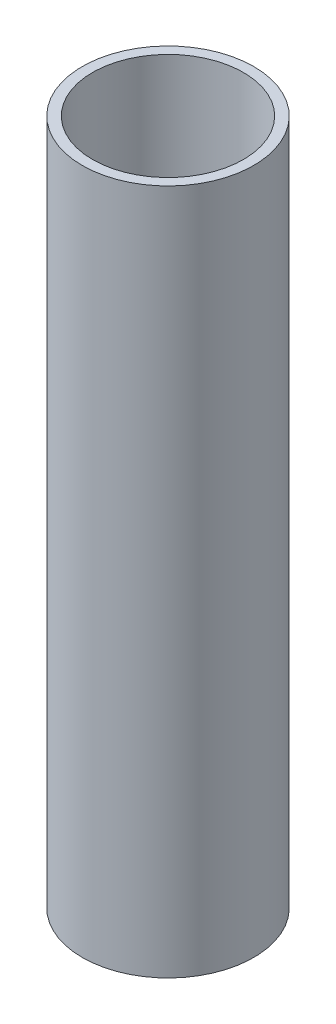
SolidWorks part; units mm, degrees
ref_plane "Front Plane" through (0, 0, 0) normal (0, 0, 1) x (1, 0, 0)
ref_plane "Top Plane" through (0, 0, 0) normal (0, 1, 0) x (1, 0, 0)
ref_plane "Right Plane" through (0, 0, 0) normal (1, 0, 0) x (0, 0, -1)
sketch "Sketch1" plane through (0, 0, 0) normal (0, 1, 0) x (1, 0, 0)
  circle A0 centre (0, 0) radius 12.7
  circle A1 centre (0, 0) radius 11.176
  dimension "D1" = 25.4
  dimension "D2" = 22.352
extrude "Boss-Extrude1" add sketch "Sketch1" along normal blind 101.6
